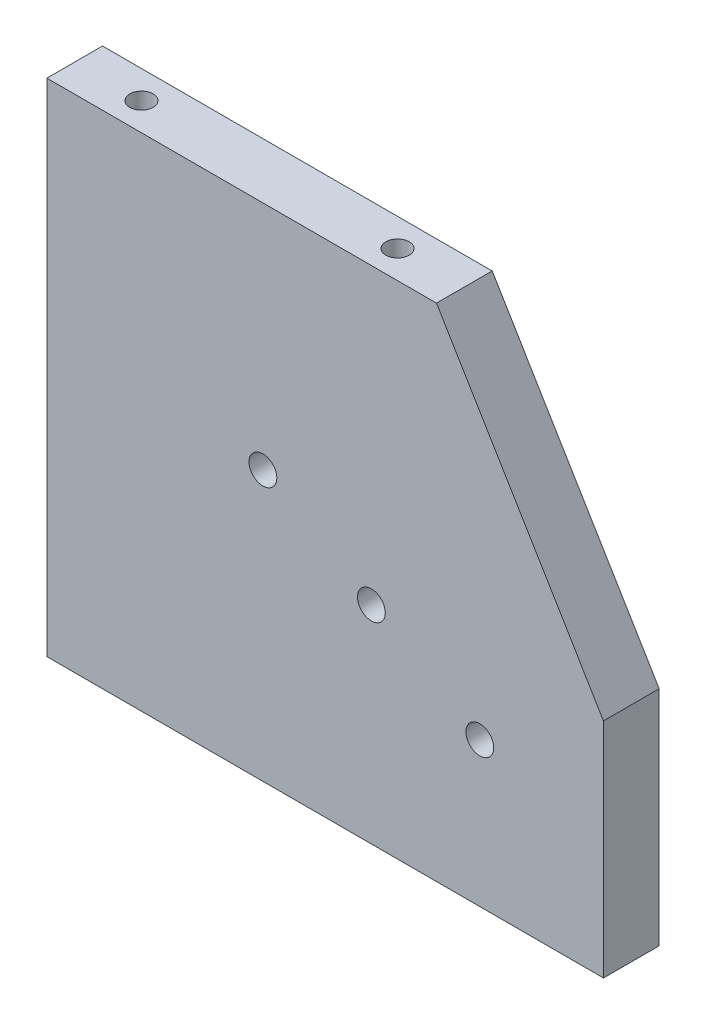
SolidWorks part; units mm, degrees
ref_plane "Front Plane" through (0, 0, 0) normal (0, 0, 1) x (1, 0, 0)
ref_plane "Top Plane" through (0, 0, 0) normal (0, 1, 0) x (1, 0, 0)
ref_plane "Right Plane" through (0, 0, 0) normal (1, 0, 0) x (0, 0, -1)
sketch "Sketch2" plane through (0, 0, 0) normal (0, 0, 1) x (1, 0, 0)
  line L0 (39.6842, 32.6842) -> (69.6842, -17.3158)
  line L1 (-30.3158, 32.6842) -> (39.6842, 32.6842)
  line L2 (-30.3158, 32.6842) -> (-30.3158, -57.3158)
  line L3 (-30.3158, -57.3158) -> (69.6842, -57.3158)
  line L4 (69.6842, -17.3158) -> (69.6842, -57.3158)
  dimension "D1" = 90
  dimension "D2" = 100
  dimension "D3" = 70
  dimension "D4" = 40
extrude "Boss-Extrude1" add sketch "Sketch2" along normal blind 10
sketch "Sketch3" plane through (0, 0, 10) normal (0, 0, 1) x (1, 0, 0)
  line L0 (27.9842, -20.1158) -> (62.4784, -40.031)
  line L1 (-30.3158, 32.6842) -> (-30.3158, -57.3158) construction
  line L2 (-30.3158, -57.3158) -> (69.6842, -57.3158) construction
  line L3 (-15.3171, 4.8842) -> (27.9842, -20.1158)
  circle A0 centre (27.9842, -20.1158) radius 22.5
  dimension "D1" = 45
  dimension "D2" = 58.3
  dimension "D3" = 37.2
  dimension "D4" = 180
  dimension "D5" = 30
hole_wizard "M6 Tapped Hole1" positions "Sketch4" profile "Sketch5" tap size "M6" standard "ISO"
sketch "Sketch4" plane through (0, 0, 10) normal (0, 0, 1) x (1, 0, 0)
  line L0 (-15.3171, 4.8842) -> (27.9842, -20.1158) construction
  line L1 (27.9842, -20.1158) -> (62.4784, -40.031) construction
  circle A0 centre (27.9842, -20.1158) radius 22.5 construction
  point P0 (8.4986, -8.8658)
  point P6 (47.4698, -31.3658)
  point P10 (27.9842, -20.1158)
  point P14 (0, 0)
  point P15 (0, 0)
sketch "Sketch5" plane through (8.4986, -8.8658, 10) normal (1, 0, 0) x (0, -1, 0)
  line L0 (0, 0) -> (0, 16.5022)
  line L1 (0, 16.5022) -> (2.5, 15)
  line L2 (2.5, 15) -> (2.5, 0)
  line L5 (2.5, 0) -> (0, 0)
  line L10 (0, 16.5022) -> (-2.5, 15) construction
  line L11 (0, -6.35) -> (0, 107.95) construction
  dimension "Tap Drill Dia." = 5
  dimension "Tap Drill Depth" = 15
  dimension "Drill Angle" = 118
cosmetic thread "Hole Thread1" parameters "D1"=10, "D2"=6
cosmetic thread "Hole Thread2" parameters "D1"=10, "D2"=6
cosmetic thread "Hole Thread3" parameters "D1"=10, "D2"=6
hole_wizard "M5 Tapped Hole1" positions "Sketch6" profile "Sketch7" tap size "M5" standard "ISO"
sketch "Sketch6" plane through (0, 32.6842, 0) normal (0, 1, 0) x (1, 0, 0)
  line L0 (-30.3158, -10) -> (-30.3158, 0) construction
  line L1 (39.6842, 0) -> (-30.3158, 0) construction
  point P0 (-18.3158, -5)
  point P2 (27.6842, -5)
  dimension "D1" = 46
  dimension "D2" = 12
  dimension "D3" = 5
sketch "Sketch7" plane through (-18.3158, 32.6842, 5) normal (1, 0, 0) x (0, 0, 1)
  line L0 (0, 0) -> (0, 9.2618)
  line L1 (0, 9.2618) -> (2.1, 8)
  line L2 (2.1, 8) -> (2.1, 0)
  line L5 (2.1, 0) -> (0, 0)
  line L10 (0, 9.2618) -> (-2.1, 8) construction
  line L11 (0, -6.35) -> (0, 107.95) construction
  dimension "Tap Drill Dia." = 4.2
  dimension "Tap Drill Depth" = 8
  dimension "Drill Angle" = 118
cosmetic thread "Hole Thread4" parameters "D1"=8, "D2"=5
cosmetic thread "Hole Thread5" parameters "D1"=8, "D2"=5
